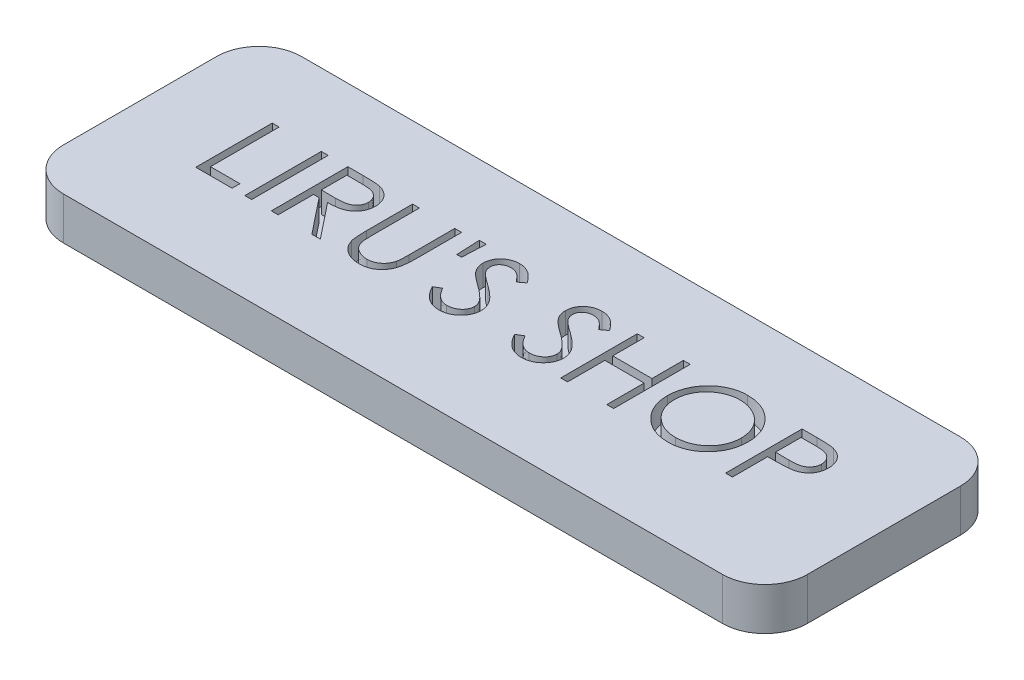
SolidWorks part; units mm, degrees
ref_plane "Front Plane" through (0, 0, 0) normal (0, 0, 1) x (1, 0, 0)
ref_plane "Top Plane" through (0, 0, 0) normal (0, 1, 0) x (1, 0, 0)
ref_plane "Right Plane" through (0, 0, 0) normal (1, 0, 0) x (0, 0, -1)
sketch "Sketch1" plane through (0, 0, 0) normal (0, 1, 0) x (1, 0, 0)
  line L1 (-87.5, 28) -> (87.5, 28)
  line L2 (-87.5, 28) -> (-87.5, -28)
  line L3 (-87.5, -28) -> (87.5, -28)
  line L4 (87.5, 28) -> (87.5, -28)
  line L5 (-87.5, 28) -> (87.5, -28) construction
  line L6 (-87.5, -28) -> (87.5, 28) construction
  point P0 (0, 0)
  dimension "D1" = 175
  dimension "D2" = 56
extrude "Boss-Extrude1" add sketch "Sketch1" along normal blind 10
sketch "Sketch2" plane through (0, 10, 0) normal (0, 1, 0) x (1, 0, 0)
  line L0 (-87.5, -7) -> (87.5, -7) construction
  line L1 (-87.5, 28) -> (-87.5, -28) construction
  line L2 (87.5, -28) -> (87.5, 28) construction
  line L3 (87.5, 28) -> (-87.5, 28) construction
  text T0 "LIRU'S SHOP" font "Century Gothic" height 18
  dimension "D1" = 35
extrude "Cut-Extrude1" cut sketch "Sketch2" against normal blind 5
fillet "Fillet1" radius 10 4 edges at (87.5, 5, 28) (87.5, 5, -28) (-87.5, 5, 28) (-87.5, 5, -28)
